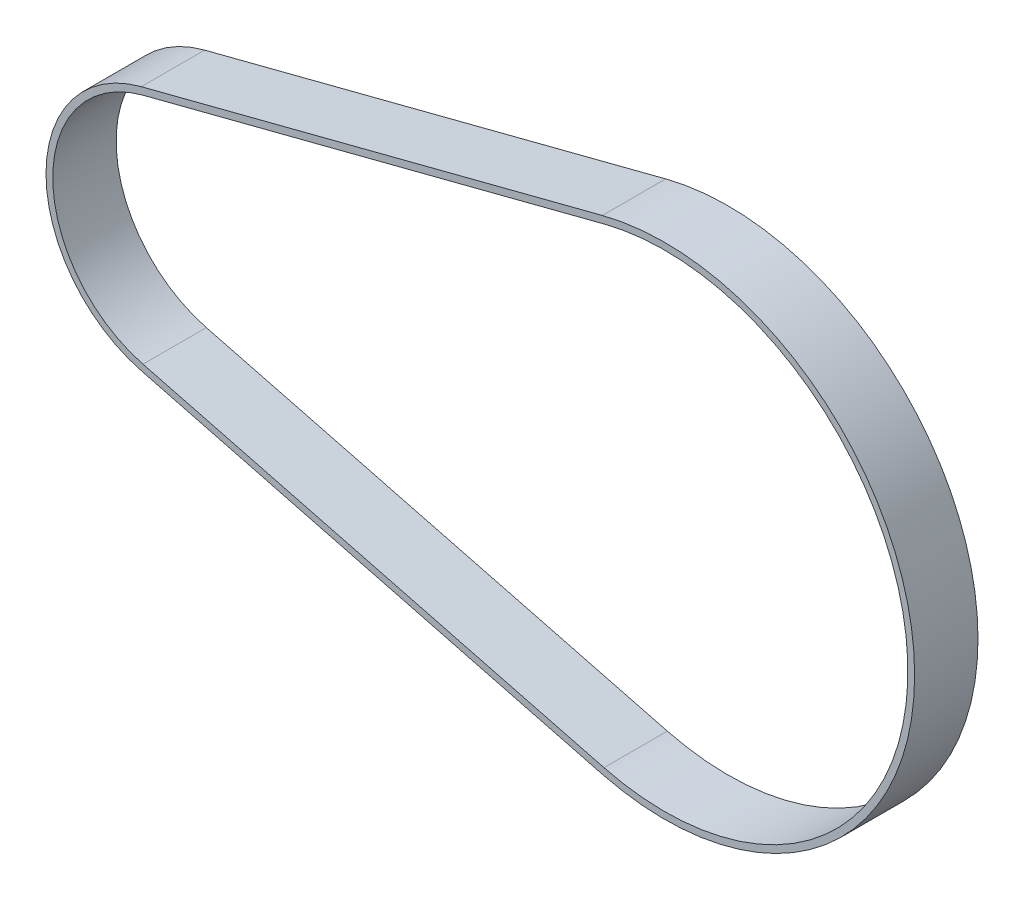
SolidWorks part; units mm, degrees
ref_plane "Front Plane" through (0, 0, 0) normal (0, 0, 1) x (1, 0, 0)
ref_plane "Top Plane" through (0, 0, 0) normal (0, 1, 0) x (1, 0, 0)
ref_plane "Right Plane" through (0, 0, 0) normal (1, 0, 0) x (0, 0, -1)
sketch "Sketch3" plane through (0, 0, 0) normal (0, 0, 1) x (1, 0, 0)
  line L0 (-48.9406, -11.0207) -> (-5.8158, -22.2784)
  line L1 (-48.9406, 11.0207) -> (-5.8158, 22.2784)
  line L4 (115.2915, 84.9196) -> (115.2915, 0.8255)
  line L5 (115.2915, 0.8255) -> (115.2915, -43.7445)
  line L6 (115.2915, -43.7445) -> (115.2915, -88.3146)
  line L7 (115.2915, -88.3146) -> (115.2915, -118.2804)
  arc A2 (-5.8158, -22.2784) -> (-5.8158, 22.2784) centre (0, 0) ccw
  arc A3 (-48.9406, 11.0207) -> (-48.9406, -11.0207) centre (-46.0637, 0) ccw
  circle A5 centre (-46.5637, 0) radius 11.39 construction
  dimension "D3" = 0.5
  dimension "D4" = 23.025
  dimension "D2" = 11.39
  dimension "D1" = 203.2
sketch "Sketch4" plane through (0, 0, 0) normal (0, 0, 1) x (1, 0, 0)
  line L0 (-49.4097, 11.0287) -> (-5.7533, 22.2946)
  line L1 (-49.4097, -11.0287) -> (-5.7533, -22.2946)
  line L2 (-49.5696, 11.6484) -> (-5.9132, 22.9143)
  line L3 (-49.5696, -11.6484) -> (-5.9132, -22.9143)
  line L4 (-46.5637, 0) -> (0, 0) construction
  line L5 (-46.5637, 0) -> (-67.665, 0) construction
  circle A0 centre (-46.5637, 0) radius 11.39 construction
  arc A1 (-49.4097, 11.0287) -> (-49.4097, -11.0287) centre (-46.5637, 0) ccw
  arc A2 (-5.7533, -22.2946) -> (-5.7533, 22.2946) centre (0, 0) ccw
  arc A3 (-5.8158, -22.2784) -> (-5.8158, 22.2784) centre (0, 0) ccw construction
  arc A4 (-5.9132, -22.9143) -> (-5.9132, 22.9143) centre (0, 0) ccw
  arc A5 (-49.5696, 11.6484) -> (-49.5696, -11.6484) centre (-46.5637, 0) ccw
  dimension "D1" = 0.64
extrude "Boss-Extrude1" add sketch "Sketch4" along normal mid plane 6
